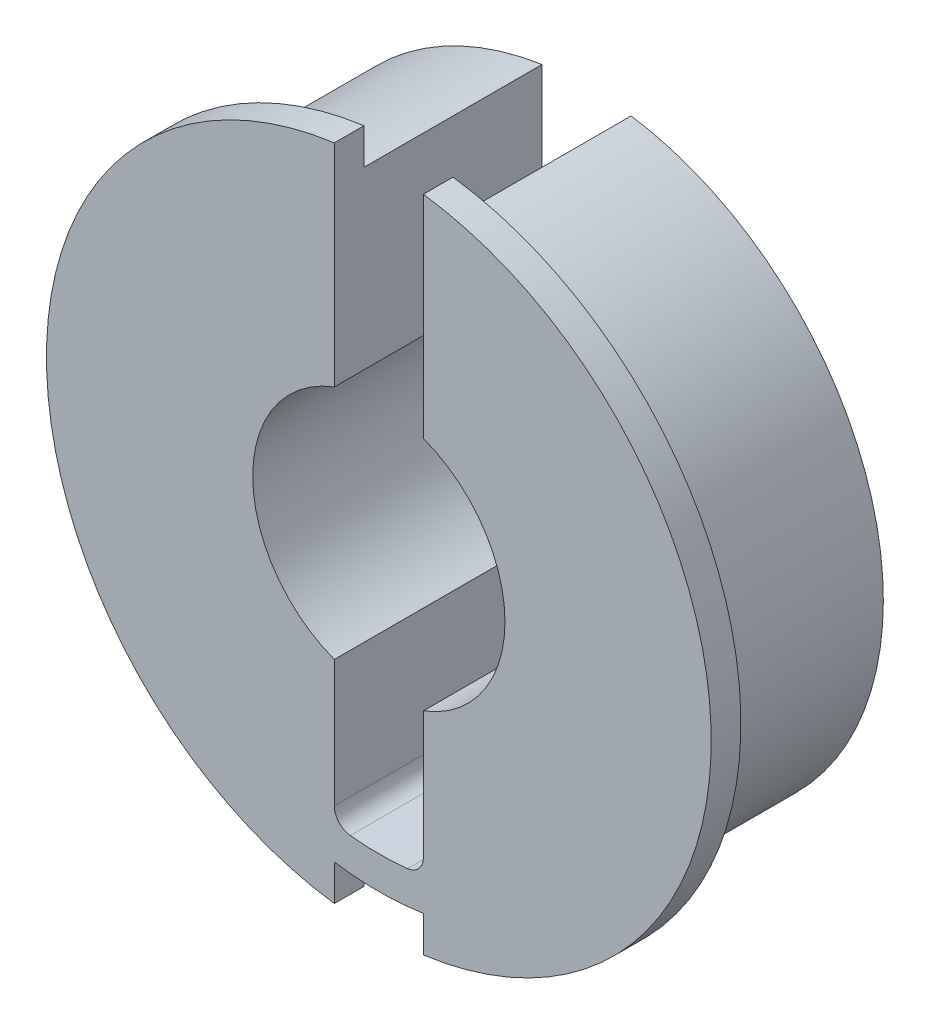
SolidWorks part; units mm, degrees
ref_plane "Front Plane" through (0, 0, 0) normal (0, 0, 1) x (1, 0, 0)
ref_plane "Top Plane" through (0, 0, 0) normal (0, 1, 0) x (1, 0, 0)
ref_plane "Right Plane" through (0, 0, 0) normal (1, 0, 0) x (0, 0, -1)
sketch "Sketch1" plane through (0, 0, 0) normal (0, 0, 1) x (1, 0, 0)
  circle A0 centre (0, 0) radius 12.7
  circle A1 centre (0, 0) radius 5.3975
  dimension "D1" = 25.4
  dimension "D2" = 10.795
extrude "Boss-Extrude1" add sketch "Sketch1" along normal blind 7.62
sketch "Sketch2" plane through (0, 0, 7.62) normal (0, 0, 1) x (1, 0, 0)
  circle A0 centre (0, 0) radius 5.3975
  circle A3 centre (0, 0) radius 5.3975 construction
  circle A4 centre (0, 0) radius 14.224
  circle A5 centre (0, 0) radius 14.224
  dimension "D1" = 1.524
extrude "Boss-Extrude2" add sketch "Sketch2" along normal blind 1.27
sketch "Sketch3" plane through (0, 0, 0) normal (0, 0, -1) x (-1, 0, 0)
  line L0 (0, 0) -> (0, 14.224) construction
  line L1 (-1.905, 14.224) -> (1.905, 14.224)
  line L2 (1.905, 14.224) -> (1.905, -11.1413)
  line L3 (-1.905, 14.224) -> (-1.905, -11.1413)
  line L4 (0, -11.303) -> (0, 0) construction
  circle A0 centre (0, 0) radius 14.224 construction
  arc A3 (-1.905, -11.1413) -> (1.905, -11.1413) centre (0, 0) ccw
  circle A4 centre (0, 0) radius 11.303
  circle A5 centre (0, 0) radius 11.303 construction
  dimension "D1" = 3.81
  dimension "D2" = 1.397
extrude "Cut-Extrude1" cut sketch "Sketch3" against normal through all
sketch "Sketch4" plane through (0, 0, 7.62) normal (0, 0, -1) x (-1, 0, 0)
  line L0 (-1.905, -14.224) -> (-1.905, -12.5563)
  line L1 (1.905, -12.5563) -> (1.905, -14.224)
  line L2 (-1.905, -5.0501) -> (-1.905, -11.1413) construction
  line L3 (1.905, -11.1413) -> (1.905, -5.0501) construction
  line L4 (-1.905, -14.224) -> (1.905, -14.224)
  arc A0 (-1.905, 12.5563) -> (1.905, 12.5563) centre (0, 0) ccw construction
  arc A1 (-1.905, 14.0959) -> (1.905, 14.0959) centre (0, 0) ccw construction
  arc A2 (-1.905, -12.5563) -> (1.905, -12.5563) centre (0, 0) ccw
extrude "Cut-Extrude2" cut sketch "Sketch4" against normal through all
fillet "Fillet1" radius 0.762 2 edges at (-1.905, -11.1413, 4.445) (1.905, -11.1413, 4.445)
